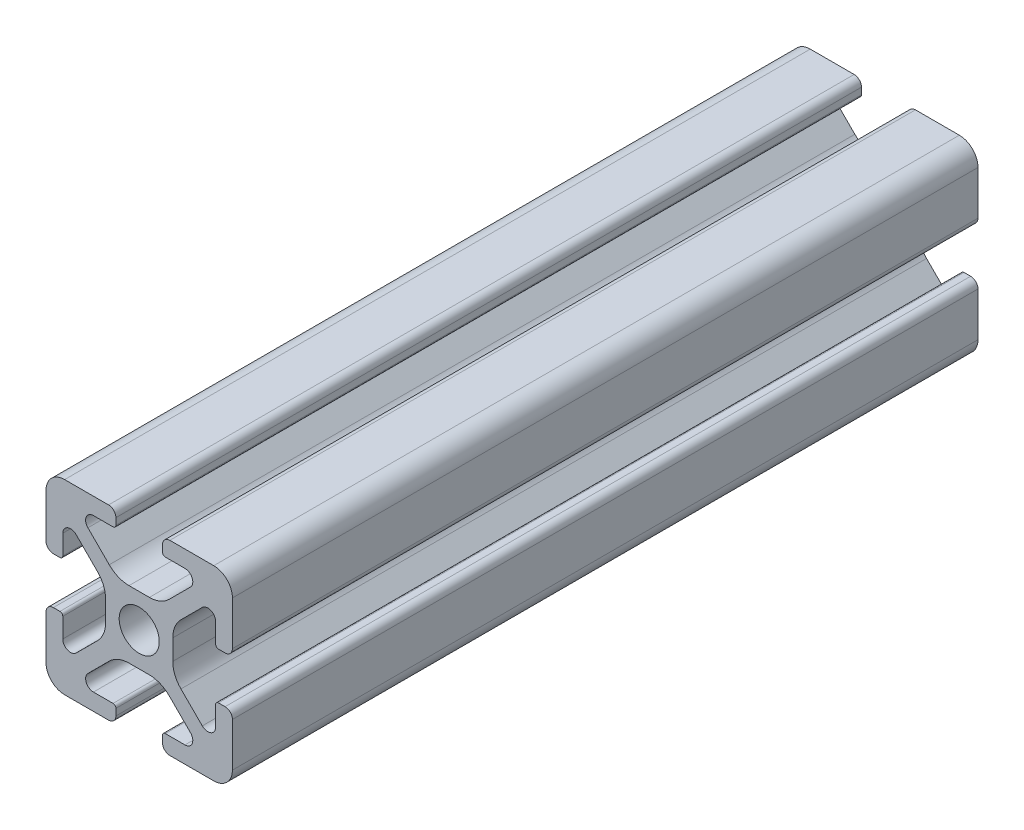
SolidWorks part; units mm, degrees
ref_plane "Front Plane" through (0, 0, 0) normal (0, 0, 1) x (1, 0, 0)
ref_plane "Top Plane" through (0, 0, 0) normal (0, 1, 0) x (1, 0, 0)
ref_plane "Right Plane" through (0, 0, 0) normal (1, 0, 0) x (0, 0, -1)
sketch "Sketch1" plane through (0, 0, 0) normal (0, 0, 1) x (1, 0, 0)
  line L0 (0, 10) -> (0, -10) construction
  line L1 (10, 0) -> (-10, 0) construction
  line L2 (-2.5, 10) -> (2.5, 10) construction
  line L3 (-5.75, 8.2) -> (5.75, 8.2) construction
  circle A0 centre (0, 0) radius 2.15 construction
  point P4 (0, 0)
  point P8 (0, 0)
  point P10 (0, 3.6)
  point P14 (0, 10)
  point P17 (0, 8.2)
  dimension "Thru Hole" = 4.3
  dimension "Height" = 20
  dimension "T Slot Depth" = 6.4
  dimension "T Slot Top Width" = 5
  dimension "T Slot Max Width" = 11.5
  dimension "Wall" = 1.8
sketch "Sketch2" plane through (0, 0, 0) normal (1, 0, 0) x (0, 0, -1)
  line L0 (40, 0) -> (-40, 0) construction
  point P4 (0, 0)
  dimension "D1" = 80
sketch "Sketch3" plane through (0, 0, 0) normal (0, 0, 1) x (1, 0, 0)
  line L0 (3.2874, 10) -> (8, 10)
  line L1 (10, 8) -> (10, -8) construction
  line L2 (8, -10) -> (-8, -10) construction
  line L3 (-10, 10) -> (10, -10) construction
  line L4 (2.5, 9.2126) -> (2.5, 8.5048)
  line L5 (-5.75, 8.2) -> (5.75, 8.2) construction
  line L6 (2.8048, 8.2) -> (4.9118, 8.2)
  line L7 (5.5045, 6.7691) -> (3.2141, 4.4787)
  line L8 (1.0928, 3.6) -> (-1.0928, 3.6)
  line L9 (0, 10) -> (0, -10) construction
  line L10 (5.75, 8.2) -> (5.75, 0) construction
  line L11 (10, 0) -> (-10, 0) construction
  line L12 (0, 0) -> (0, 10) construction
  line L13 (-2.5, 9.2126) -> (-2.5, 8.5048)
  line L14 (-5.5045, 6.7691) -> (-3.2141, 4.4787)
  line L15 (-2.8048, 8.2) -> (-4.9118, 8.2)
  line L16 (-3.2874, 10) -> (-8, 10)
  line L17 (0, 0) -> (-10, 0) construction
  line L18 (-10, 3.2874) -> (-10, 8)
  line L19 (-8.2, 2.8048) -> (-8.2, 4.9118)
  line L20 (-6.7691, 5.5045) -> (-4.4787, 3.2141)
  line L21 (-9.2126, 2.5) -> (-8.5048, 2.5)
  line L22 (-3.6, -1.0928) -> (-3.6, 1.0928)
  line L23 (-6.7691, -5.5045) -> (-4.4787, -3.2141)
  line L24 (-8.2, -2.8048) -> (-8.2, -4.9118)
  line L25 (-9.2126, -2.5) -> (-8.5048, -2.5)
  line L26 (-10, -3.2874) -> (-10, -8)
  line L27 (9.2126, -2.5) -> (8.5048, -2.5)
  line L28 (8.2, -2.8048) -> (8.2, -4.9118)
  line L29 (6.7691, -5.5045) -> (4.4787, -3.2141)
  line L30 (3.6, -1.0928) -> (3.6, 1.0928)
  line L31 (9.2126, 2.5) -> (8.5048, 2.5)
  line L32 (6.7691, 5.5045) -> (4.4787, 3.2141)
  line L33 (8.2, 2.8048) -> (8.2, 4.9118)
  line L34 (10, 8) -> (10, 3.2874)
  line L35 (10, -3.2874) -> (10, -8)
  line L36 (3.2874, -10) -> (8, -10)
  line L37 (-3.2874, -10) -> (-8, -10)
  line L38 (-6.7691, -5.5045) -> (-4.4787, -3.2141)
  line L39 (-2.8048, -8.2) -> (-4.9118, -8.2)
  line L40 (-5.5045, -6.7691) -> (-3.2141, -4.4787)
  line L41 (-2.5, -9.2126) -> (-2.5, -8.5048)
  line L42 (1.0928, -3.6) -> (-1.0928, -3.6)
  line L43 (5.5045, -6.7691) -> (3.2141, -4.4787)
  line L44 (2.8048, -8.2) -> (4.9118, -8.2)
  line L45 (2.5, -9.2126) -> (2.5, -8.5048)
  arc A0 (4.9118, 8.2) -> (5.5045, 6.7691) centre (4.9118, 7.3618) cw
  arc A1 (3.2141, 4.4787) -> (1.0928, 3.6) centre (1.0928, 6.6) cw
  circle A2 centre (0, 0) radius 2.15 construction
  circle A3 centre (0, 0) radius 2.15
  arc A4 (3.2874, 10) -> (2.5, 9.2126) centre (3.2874, 9.2126) ccw
  arc A5 (2.5, 8.5048) -> (2.8048, 8.2) centre (2.8048, 8.5048) ccw
  arc A6 (-3.2874, 10) -> (-2.5, 9.2126) centre (-3.2874, 9.2126) cw
  arc A7 (-4.9118, 8.2) -> (-5.5045, 6.7691) centre (-4.9118, 7.3618) ccw
  arc A8 (-3.2141, 4.4787) -> (-1.0928, 3.6) centre (-1.0928, 6.6) ccw
  arc A9 (-2.5, 8.5048) -> (-2.8048, 8.2) centre (-2.8048, 8.5048) cw
  arc A10 (-8.5048, 2.5) -> (-8.2, 2.8048) centre (-8.5048, 2.8048) ccw
  arc A11 (-4.4787, 3.2141) -> (-3.6, 1.0928) centre (-6.6, 1.0928) cw
  arc A12 (-8.2, 4.9118) -> (-6.7691, 5.5045) centre (-7.3618, 4.9118) cw
  arc A13 (-10, 3.2874) -> (-9.2126, 2.5) centre (-9.2126, 3.2874) ccw
  arc A14 (-8.5048, -2.5) -> (-8.2, -2.8048) centre (-8.5048, -2.8048) cw
  arc A15 (-10, -3.2874) -> (-9.2126, -2.5) centre (-9.2126, -3.2874) cw
  arc A16 (-4.4787, -3.2141) -> (-3.6, -1.0928) centre (-6.6, -1.0928) ccw
  arc A17 (-8.2, -4.9118) -> (-6.7691, -5.5045) centre (-7.3618, -4.9118) ccw
  arc A26 (-8, -10) -> (-10, -8) centre (-8, -8) cw
  arc A27 (-8, 10) -> (-10, 8) centre (-8, 8) ccw
  arc A28 (8, 10) -> (10, 8) centre (8, 8) cw
  arc A29 (10, -8) -> (8, -10) centre (8, -8) cw
  arc A30 (8.2, -4.9118) -> (6.7691, -5.5045) centre (7.3618, -4.9118) cw
  arc A31 (4.4787, -3.2141) -> (3.6, -1.0928) centre (6.6, -1.0928) cw
  arc A32 (10, -3.2874) -> (9.2126, -2.5) centre (9.2126, -3.2874) ccw
  arc A33 (8.5048, -2.5) -> (8.2, -2.8048) centre (8.5048, -2.8048) ccw
  arc A34 (10, 3.2874) -> (9.2126, 2.5) centre (9.2126, 3.2874) cw
  arc A35 (8.2, 4.9118) -> (6.7691, 5.5045) centre (7.3618, 4.9118) ccw
  arc A36 (4.4787, 3.2141) -> (3.6, 1.0928) centre (6.6, 1.0928) ccw
  arc A37 (8.5048, 2.5) -> (8.2, 2.8048) centre (8.5048, 2.8048) cw
  arc A38 (-2.5, -8.5048) -> (-2.8048, -8.2) centre (-2.8048, -8.5048) ccw
  arc A39 (-3.2141, -4.4787) -> (-1.0928, -3.6) centre (-1.0928, -6.6) cw
  arc A40 (-4.9118, -8.2) -> (-5.5045, -6.7691) centre (-4.9118, -7.3618) cw
  arc A41 (-3.2874, -10) -> (-2.5, -9.2126) centre (-3.2874, -9.2126) ccw
  arc A42 (2.5, -8.5048) -> (2.8048, -8.2) centre (2.8048, -8.5048) cw
  arc A43 (3.2874, -10) -> (2.5, -9.2126) centre (3.2874, -9.2126) cw
  arc A44 (3.2141, -4.4787) -> (1.0928, -3.6) centre (1.0928, -6.6) ccw
  arc A45 (4.9118, -8.2) -> (5.5045, -6.7691) centre (4.9118, -7.3618) ccw
  point P36 (2.5, 10)
  point P39 (2.5, 8.2)
  point P49 (0, 3.6)
  point P77 (-3.6, 0)
  point P78 (-8.2, -2.5)
  point P79 (-10, -2.5)
  point P104 (-10, -10)
  point P110 (10, 10)
  point P114 (10, -2.5)
  point P115 (8.2, -2.5)
  point P116 (3.6, 0)
  point P141 (0, -3.6)
  dimension "D1" = 3
  dimension "D2" = 0.8382
  dimension "D4" = 0.7874
  dimension "D5" = 0.3048
  dimension "D6" = 2
  dimension "D3" = 45
extrude "Boss-Extrude1" add sketch "Sketch3" along normal up to vertex (40 mm away) and the other way up to vertex (40 mm away) contours A45 L44 A42 L45 A43 L36 A29 L35 A32 L27 A33 L28 A30 L29 A31 L30 A36 L32 A35 L33 A37 L31 A34 L34 A28 L0 A4 L4 A5 L6 A0 L7 A1 L8 A8 L14 A7 L15 A9 L13 A6 L16 A27 L18 A13 L21 A10 L19 A12 L20 A11 up to point (0, 0, 40) other way up to point (0, 0, -40)
